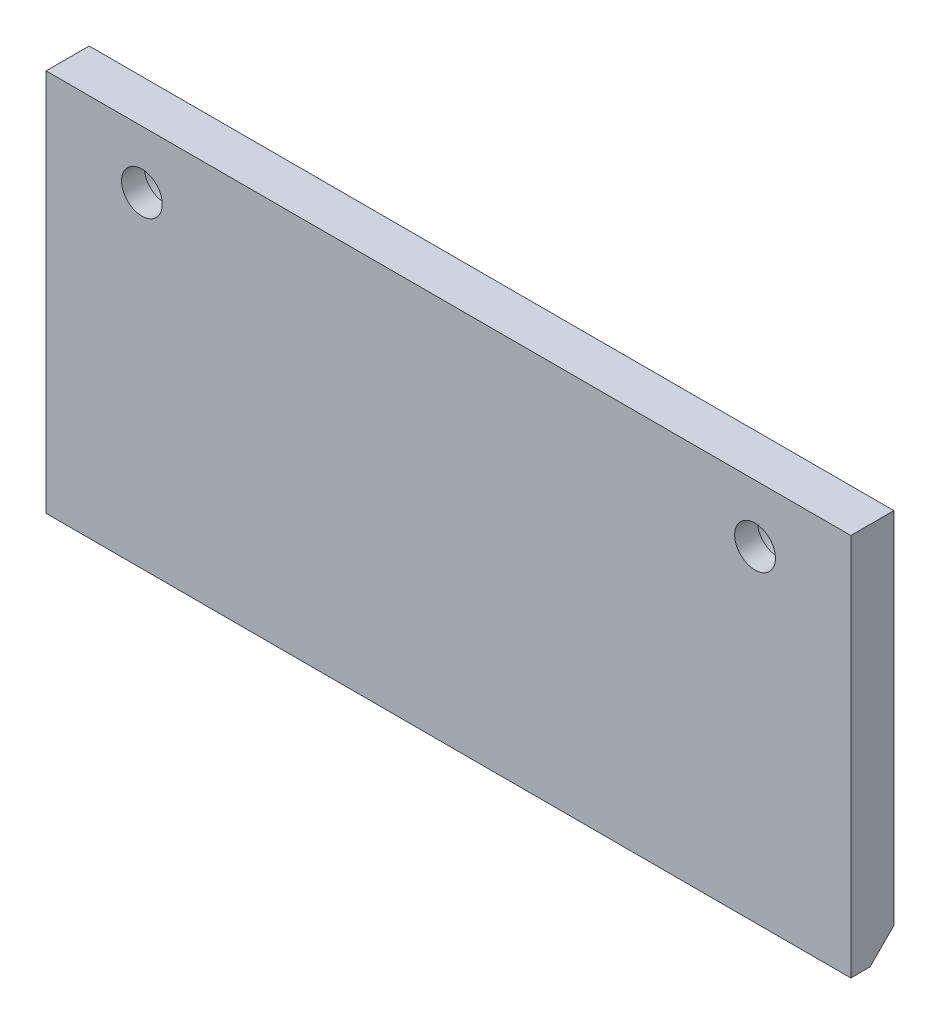
SolidWorks part; units mm, degrees
material "AISI 1020 Steel, Cold Rolled"
ref_plane "Front" through (0, 0, 0) normal (0, 0, 1) x (1, 0, 0)
ref_plane "Top" through (0, 0, 0) normal (0, 1, 0) x (1, 0, 0)
ref_plane "Right" through (0, 0, 0) normal (1, 0, 0) x (0, 0, -1)
sketch "Sketch1" plane through (0, 0, 0) normal (0, 0, 1) x (1, 0, 0)
  line L1 (66.675, 31.75) -> (-66.675, 31.75)
  line L2 (66.675, 31.75) -> (66.675, -31.75)
  line L3 (66.675, -31.75) -> (-66.675, -31.75)
  line L4 (-66.675, 31.75) -> (-66.675, -31.75)
  line L5 (66.675, 31.75) -> (-66.675, -31.75) construction
  line L6 (66.675, -31.75) -> (-66.675, 31.75) construction
  point P0 (0, 0)
  dimension "D1" = 133.35
  dimension "D2" = 63.5
extrude "Boss-Extrude1" add sketch "Sketch1" against normal mid plane 7.1374
sketch "Sketch2" plane through (-66.675, 0, 0) normal (-1, 0, 0) x (0, 0, 1)
  line L0 (0.3937, -31.75) -> (-3.5687, -27.7876)
  line L1 (-3.5687, -31.75) -> (3.5687, -31.75) construction
  line L2 (-3.5687, 31.75) -> (-3.5687, -31.75) construction
  line L3 (3.5687, 31.75) -> (3.5687, -31.75) construction
  line L4 (-3.5687, -27.7876) -> (-3.5687, -31.75)
  line L5 (-3.5687, -31.75) -> (0.3937, -31.75)
  dimension "D1" = 3.175
  dimension "D2" = 45
extrude "Cut-Extrude1" cut sketch "Sketch2" against normal through all
hole_wizard "CBORE for 1/4 Button Head Cap Screw1" positions "Sketch3" profile "Sketch4" counterbore size "1/4" standard "ANSI Inch" end condition through all
sketch "Sketch3" plane through (0, 0, -3.5687) normal (0, 0, -1) x (-1, 0, 0)
  line L1 (-66.675, -27.7876) -> (-66.675, 31.75) construction
  line L2 (-66.675, 31.75) -> (66.675, 31.75) construction
  line L3 (66.675, 31.75) -> (66.675, -27.7876) construction
  point P0 (-50.8, 22.225)
  point P2 (50.8, 22.225)
  dimension "D1" = 15.875
  dimension "D2" = 15.875
  dimension "D3" = 9.525
sketch "Sketch4" plane through (50.8, 22.225, -3.5687) normal (1, 0, 0) x (0, 1, 0)
  line L0 (0, 0) -> (0, 7.1374)
  line L1 (0, 7.1374) -> (3.3782, 7.1374)
  line L3 (3.3782, 7.1374) -> (3.3782, 3.3528)
  line L4 (3.3782, 3.3528) -> (5.9538, 3.3528)
  line L5 (5.9538, 3.3528) -> (5.9538, 0)
  line L7 (5.9538, 0) -> (0, 0)
  line L11 (0, -6.35) -> (0, 107.95) construction
  dimension "Thru Hole Dia." = 6.7564
  dimension "Thru Hole Depth" = 7.1374
  dimension "C'Bore Dia." = 11.9075
  dimension "C'Bore Depth" = 3.3528
